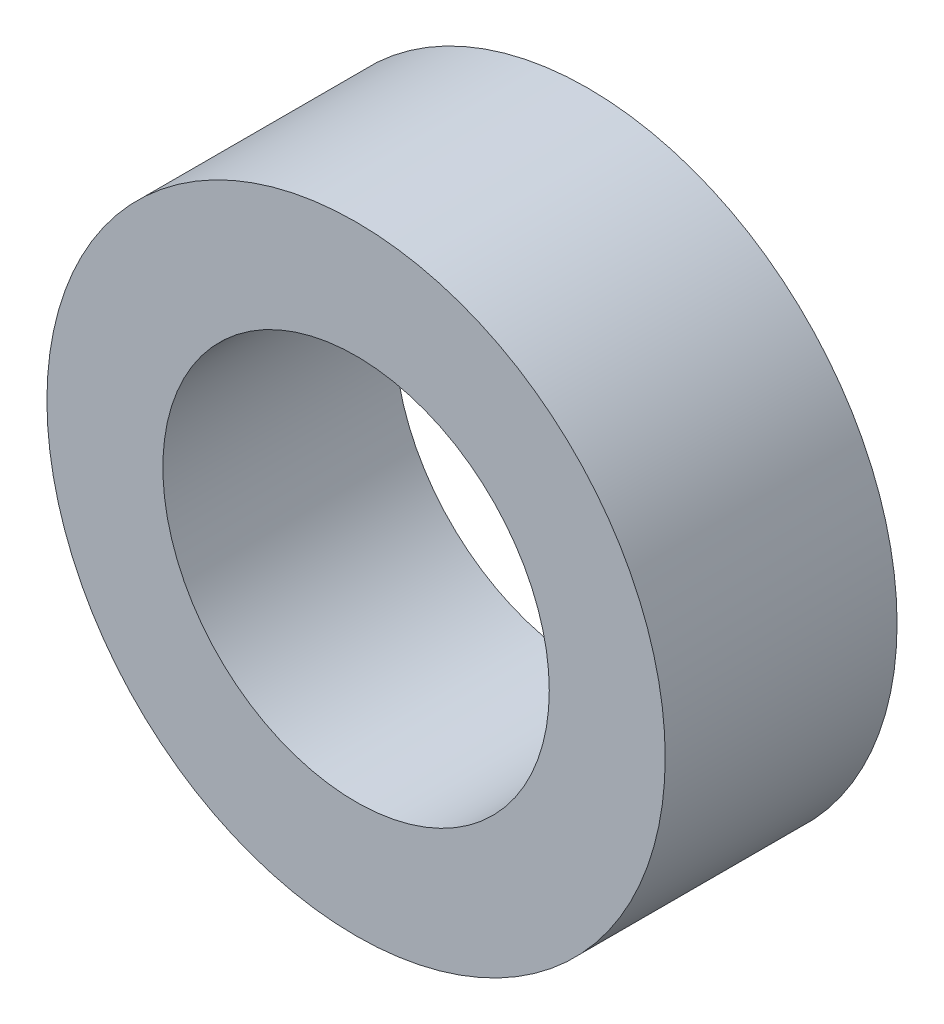
SolidWorks part; units mm, degrees
material "瞎编数据的PLA"
ref_plane "前视基准面" through (0, 0, 0) normal (0, 0, 1) x (1, 0, 0)
ref_plane "上视基准面" through (0, 0, 0) normal (0, 1, 0) x (1, 0, 0)
ref_plane "右视基准面" through (0, 0, 0) normal (1, 0, 0) x (0, 0, -1)
sketch "草图1" plane through (0, 0, 0) normal (0, 0, 1) x (1, 0, 0)
  circle A0 centre (0, 0) radius 2.5
  circle A1 centre (0, 0) radius 4
  dimension "D1" = 5
  dimension "D2" = 8
extrude "凸台-拉伸1" add sketch "草图1" along normal blind 3
